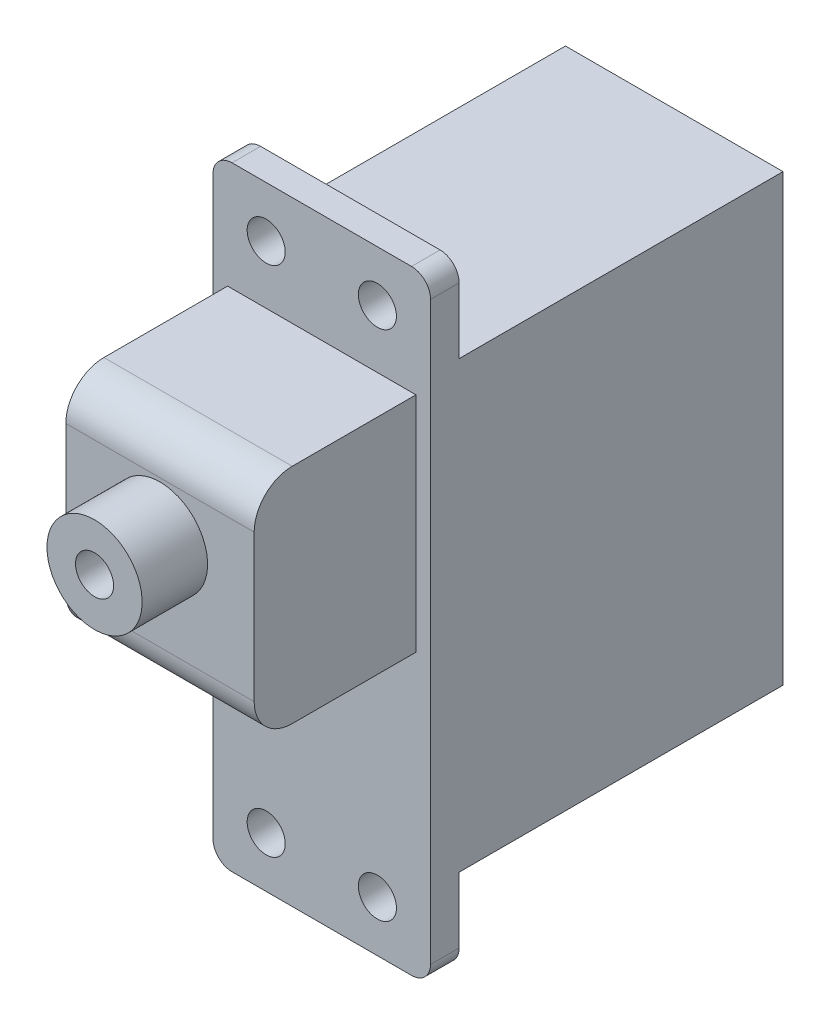
SolidWorks part; units mm, degrees
ref_plane "Plan de face" through (0, 0, 0) normal (0, 0, 1) x (1, 0, 0)
ref_plane "Plan de dessus" through (0, 0, 0) normal (0, 1, 0) x (1, 0, 0)
ref_plane "Plan de droite" through (0, 0, 0) normal (1, 0, 0) x (0, 0, -1)
ref_plane "Plan1" through (11.43, 0, 0) normal (1, 0, 0) x (0, 0, -1)
sketch "Esquisse1" plane through (11.43, 0, 0) normal (1, 0, 0) x (0, 0, -1)
  line L0 (-1.5, -4.445) -> (17.018, -4.445)
  line L1 (17.018, -4.445) -> (17.018, 27.813)
  line L2 (17.018, 27.813) -> (-1.5, 27.813)
  line L3 (-1.5, 27.813) -> (-1.5, -4.445)
extrude "Boss.-Extru.1" add sketch "Esquisse1" against normal blind 11.43
sketch "Esquisse2" plane through (0, 0, 0) normal (-1, 0, 0) x (0, 0, 1)
  line L0 (0, 0) -> (-17.018, 0)
  line L1 (-17.018, 0) -> (-17.018, -4.445)
  line L2 (-17.018, -4.445) -> (0, -4.445)
  line L3 (0, -4.445) -> (0, 0)
extrude "Enlèv. mat.-Extru.1" cut sketch "Esquisse2" against normal through all
sketch "Esquisse3" plane through (0, 0, 0) normal (-1, 0, 0) x (0, 0, 1)
  line L0 (-17.018, 23.368) -> (0, 23.368)
  line L1 (0, 23.368) -> (0, 27.813)
  line L2 (0, 27.813) -> (-17.018, 27.813)
  line L3 (-17.018, 27.813) -> (-17.018, 23.368)
extrude "Enlèv. mat.-Extru.2" cut sketch "Esquisse3" against normal through all
sketch "Esquisse4" plane through (0, 0, 1.5) normal (0, 0, 1) x (1, 0, 0)
  line L0 (0.7681, 22.0878) -> (10.6619, 22.0878)
  line L1 (10.6619, 22.0878) -> (10.6619, 10.3767)
  line L2 (10.6619, 10.3767) -> (0.7681, 10.3767)
  line L3 (0.7681, 10.3767) -> (0.7681, 22.0878)
extrude "Boss.-Extru.2" add sketch "Esquisse4" along normal blind 8.5
ref_plane "Plan2" through (0, 17.399, 0) normal (0, -1, 0) x (1, 0, 0)
sketch "Esquisse5" plane through (0, 17.399, 0) normal (0, -1, 0) x (1, 0, 0)
  line L0 (8.215, 13.438) -> (5.715, 13.438)
  line L1 (5.715, 13.438) -> (5.715, 10)
  line L2 (5.715, 10) -> (8.215, 10)
  line L3 (8.215, 10) -> (8.215, 13.438)
  line L4 (5.715, 13.438) -> (5.715, 10) construction
revolve "Révolution1" add sketch "Esquisse5" angle 360 about L4
hole_wizard "Diamètre du perçage Ø2.0 (2)1" positions "Esquisse7" profile "Esquisse6" hole size "Ø2.0" standard "Ansi Métrique"
sketch "Esquisse7" plane through (0, 0, 13.438) normal (0, 0, 1) x (1, 0, 0)
  point P0 (5.715, 17.399)
sketch "Esquisse6" plane through (5.715, 17.399, 13.438) normal (1, 0, 0) x (0, -1, 0)
  line L0 (0, 0) -> (0, 2)
  line L1 (0, 2) -> (1, 2)
  line L2 (1, 2) -> (1, 0)
  line L5 (1, 0) -> (0, 0)
  line L10 (0, 2) -> (-1, 2) construction
  line L11 (0, -6.35) -> (0, 107.95) construction
  dimension "Diamètre du perçage" = 2
  dimension "Profondeur du perçage" = 2
  dimension "Angle de pointe" = 180
hole_wizard "Diamètre du perçage Ø2.0 (2)2" positions "Esquisse9" profile "Esquisse8" hole size "Ø2.0" standard "Ansi Métrique"
sketch "Esquisse9" plane through (0, 0, 0) normal (0, 0, -1) x (-1, 0, 0)
  point P0 (-2.794, -1.778)
  point P1 (-8.636, -1.778)
  point P2 (-8.636, 25.146)
  point P3 (-2.794, 25.146)
sketch "Esquisse8" plane through (2.794, -1.778, 0) normal (1, 0, 0) x (0, 1, 0)
  line L0 (0, 0) -> (0, 13.438)
  line L1 (0, 13.438) -> (1, 13.438)
  line L2 (1, 13.438) -> (1, 0)
  line L5 (1, 0) -> (0, 0)
  line L11 (0, -6.35) -> (0, 107.95) construction
  dimension "Diamètre du perçage jusqu'au prochain" = 2
  dimension "Profondeur du perçage jusqu'au prochain" = 13.438
fillet "Congé1" radius 1 4 edges at (11.43, -4.445, 0.75) (0, 27.813, 0.75) (11.43, 27.813, 0.75) (0, -4.445, 0.75)
fillet "Congé2" radius 2 2 edges at (5.715, 10.3767, 10) (5.715, 22.0878, 10)
